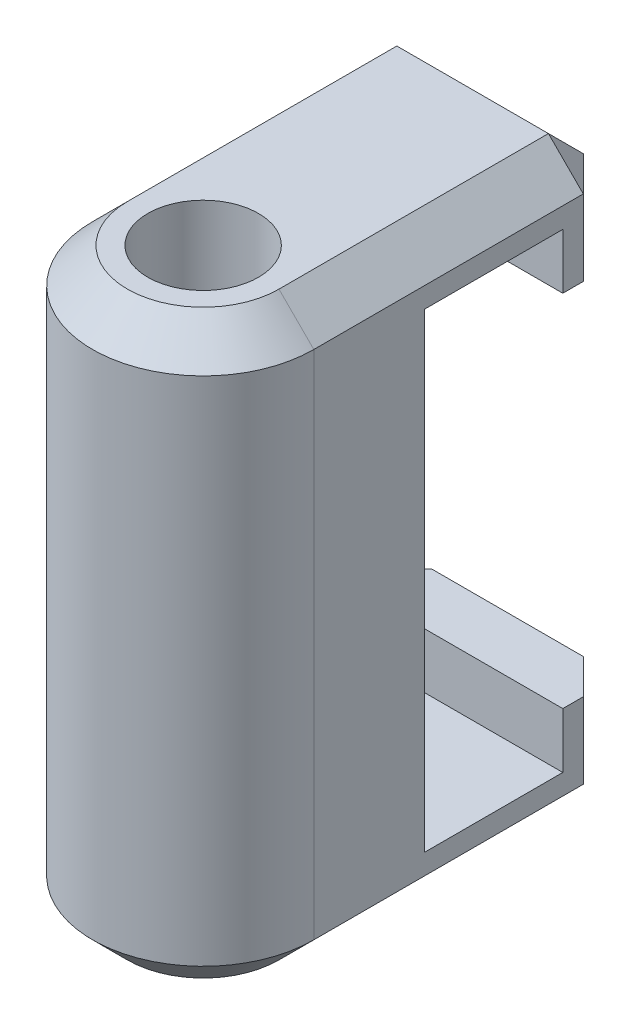
SolidWorks part; units mm, degrees
ref_plane "Front Plane" through (0, 0, 0) normal (0, 0, 1) x (1, 0, 0)
ref_plane "Top Plane" through (0, 0, 0) normal (0, 1, 0) x (1, 0, 0)
ref_plane "Right Plane" through (0, 0, 0) normal (1, 0, 0) x (0, 0, -1)
sketch "Sketch1" plane through (0, 0, 0) normal (0, 1, 0) x (1, 0, 0)
  line L0 (-3.175, 0) -> (-3.175, 8.7312)
  line L1 (-3.175, 8.7312) -> (3.175, 8.7312)
  line L2 (3.175, 8.7312) -> (3.175, 0)
  circle A0 centre (0, 0) radius 1.5875
  circle A1 centre (0, 0) radius 3.175 construction
  arc A2 (-3.175, 0) -> (3.175, 0) centre (0, 0) ccw
  dimension "D1" = 3.175
  dimension "D2" = 1.5875
  dimension "D3" = 8.7312
extrude "Boss-Extrude1" add sketch "Sketch1" along normal blind 16.6687
sketch "Sketch3" plane through (3.175, 0, 0) normal (1, 0, 0) x (0, 0, -1)
  line L0 (8.7312, 13.4937) -> (7.1437, 13.4937)
  line L1 (8.7312, 16.6687) -> (8.7312, 0) construction
  line L2 (7.1437, 13.4937) -> (7.1438, 15.0813)
  line L3 (7.1438, 15.0813) -> (3.175, 15.0813)
  line L4 (3.175, 15.0813) -> (3.175, 1.5875)
  line L5 (3.175, 1.5875) -> (7.1438, 1.5875)
  line L6 (7.1438, 1.5875) -> (7.1438, 3.175)
  line L7 (7.1438, 3.175) -> (8.7312, 3.175)
  line L8 (8.7312, 3.175) -> (8.7312, 13.4937)
  line L9 (0, 16.6687) -> (8.7312, 16.6687) construction
  dimension "D1" = 1.5875
  dimension "D2" = 3.9688
  dimension "D3" = 13.4937
  dimension "D4" = 1.5875
  dimension "D5" = 1.5875
extrude "Cut-Extrude1" cut sketch "Sketch3" against normal through all
chamfer "Chamfer1" distance 1 angle 45 12 edges at (3.175, 1.5875, -8.7312) (-3.175, 1.5875, -8.7312) (0, 0, -8.7312) (-3.175, 0, -4.3656) (0, 0, 3.175) (3.175, 0, -4.3656) (-3.175, 15.0812, -8.7312) (3.175, 15.0812, -8.7312) (0, 16.6687, -8.7312) (-3.175, 16.6687, -4.3656) (0, 16.6687, 3.175) (3.175, 16.6687, -4.3656)
